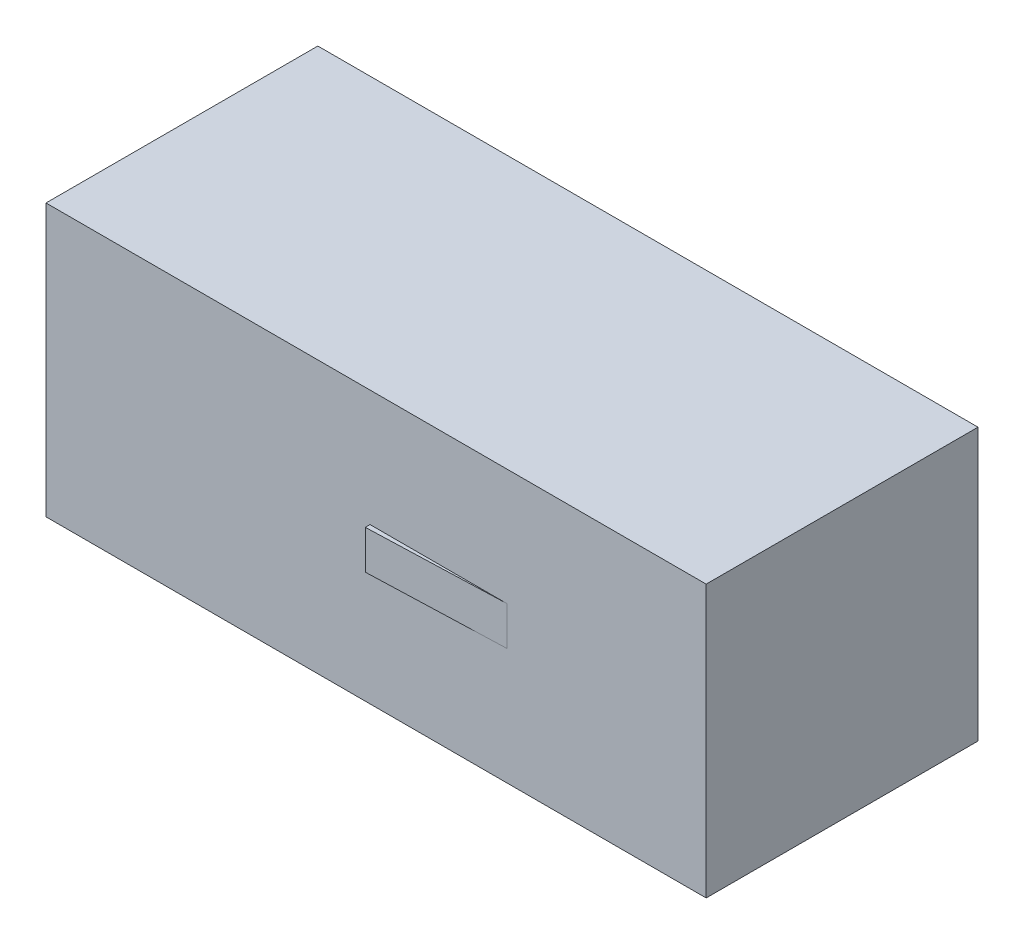
SolidWorks part; units mm, degrees
ref_plane "Front Plane" through (0, 0, 0) normal (0, 0, 1) x (1, 0, 0)
ref_plane "Top Plane" through (0, 0, 0) normal (0, 1, 0) x (1, 0, 0)
ref_plane "Right Plane" through (0, 0, 0) normal (1, 0, 0) x (0, 0, -1)
sketch "Эскиз1" plane through (0, 0, 0) normal (0, 0, 1) x (1, 0, 0)
  line L1 (-85, -35) -> (85, -35)
  line L2 (-85, -35) -> (-85, 35)
  line L3 (-85, 35) -> (85, 35)
  line L4 (85, -35) -> (85, 35)
  line L5 (-85, -35) -> (85, 35) construction
  line L6 (-85, 35) -> (85, -35) construction
  point P0 (0, 0)
  dimension "D1" = 70
  dimension "D2" = 170
extrude "Бобышка-Вытянуть1" add sketch "Эскиз1" along normal mid plane 70
sketch "Эскиз2" plane through (0, -35, 0) normal (0, -1, 0) x (1, 0, 0)
  line L0 (33.7136, 35) -> (-1.569, 35)
  line L1 (-85, 35) -> (85, 35) construction
  line L3 (-1.526, 36.2306) -> (33.7136, 35)
  line L6 (-1.526, 36.2306) -> (-1.569, 35)
  dimension "D1" = 2
  dimension "D2" = 90
extrude "Бобышка-Вытянуть2" add sketch "Эскиз2" along normal mid plane 10 from offset 35
